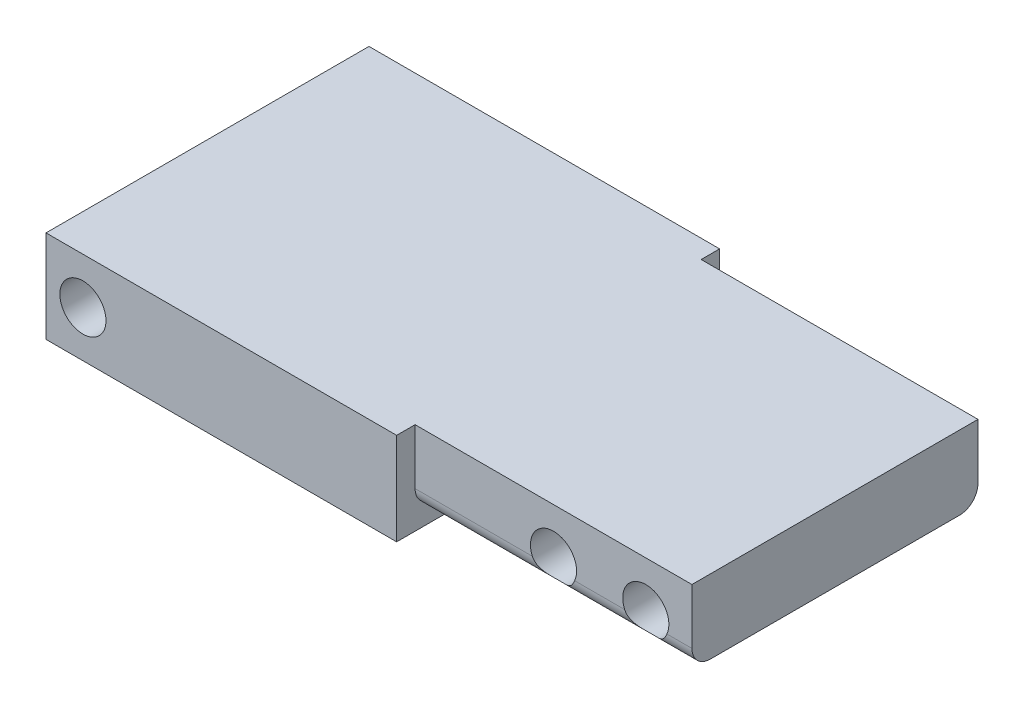
SolidWorks part; units mm, degrees
ref_plane "Front Plane" through (0, 0, 0) normal (0, 0, 1) x (1, 0, 0)
ref_plane "Top Plane" through (0, 0, 0) normal (0, 1, 0) x (1, 0, 0)
ref_plane "Right Plane" through (0, 0, 0) normal (1, 0, 0) x (0, 0, -1)
sketch "Sketch1" plane through (0, 0, 0) normal (1, 0, 0) x (0, 0, -1)
  line L1 (-74.2718, 53.1341) -> (-39.2718, 53.1341)
  line L2 (-74.2718, 53.1341) -> (-74.2718, 43.1341)
  line L3 (-74.2718, 43.1341) -> (-39.2718, 43.1341)
  line L4 (-39.2718, 53.1341) -> (-39.2718, 43.1341)
  dimension "D1" = 35
  dimension "D2" = 10
extrude "Extrude1" add sketch "Sketch1" along normal blind 38
sketch "Sketch2" plane through (38, 0, 0) normal (1, 0, 0) x (0, 0, -1)
  line L0 (-39.2718, 53.1341) -> (-74.2718, 53.1341) construction
  line L1 (-74.2718, 53.1341) -> (-74.2718, 43.1341) construction
  line L2 (-72.2718, 53.1341) -> (-41.2718, 53.1341)
  line L3 (-72.2718, 53.1341) -> (-72.2718, 45.1341)
  line L4 (-72.2718, 45.1341) -> (-41.2718, 45.1341)
  line L5 (-41.2718, 53.1341) -> (-41.2718, 45.1341)
  line L6 (-74.2718, 43.1341) -> (-39.2718, 43.1341) construction
  line L7 (-39.2718, 43.1341) -> (-39.2718, 53.1341) construction
  dimension "D1" = 2
  dimension "D2" = 2
  dimension "D3" = 2
extrude "Extrude2" add sketch "Sketch2" along normal blind 30
fillet "Fillet1" radius 2 2 edges at (53, 45.1341, 72.2718) (53, 45.1341, 41.2718)
sketch "Sketch3" plane through (0, 0, 41.2718) normal (0, 0, -1) x (-1, 0, 0)
  line L0 (-38, 43.1341) -> (0, 43.1341) construction
  line L1 (-68, 47.1341) -> (-68, 53.1341) construction
  circle A0 centre (-63, 48.1341) radius 2.5
  circle A1 centre (-53, 48.1341) radius 2.5
  dimension "D2" = 5
  dimension "D4" = 5
  dimension "D1" = 5
  dimension "D3" = 5
  dimension "D5" = 5
  dimension "D6" = 10
extrude "Extrude3" cut sketch "Sketch3" against normal through all
sketch "Sketch4" plane through (0, 0, 39.2718) normal (0, 0, -1) x (-1, 0, 0)
  line L0 (0, 43.1341) -> (0, 53.1341) construction
  line L1 (-38, 43.1341) -> (0, 43.1341) construction
  circle A0 centre (-4, 48.1341) radius 2.5
  dimension "D3" = 5
  dimension "D1" = 4
  dimension "D2" = 5
extrude "Extrude4" cut sketch "Sketch4" against normal through all
